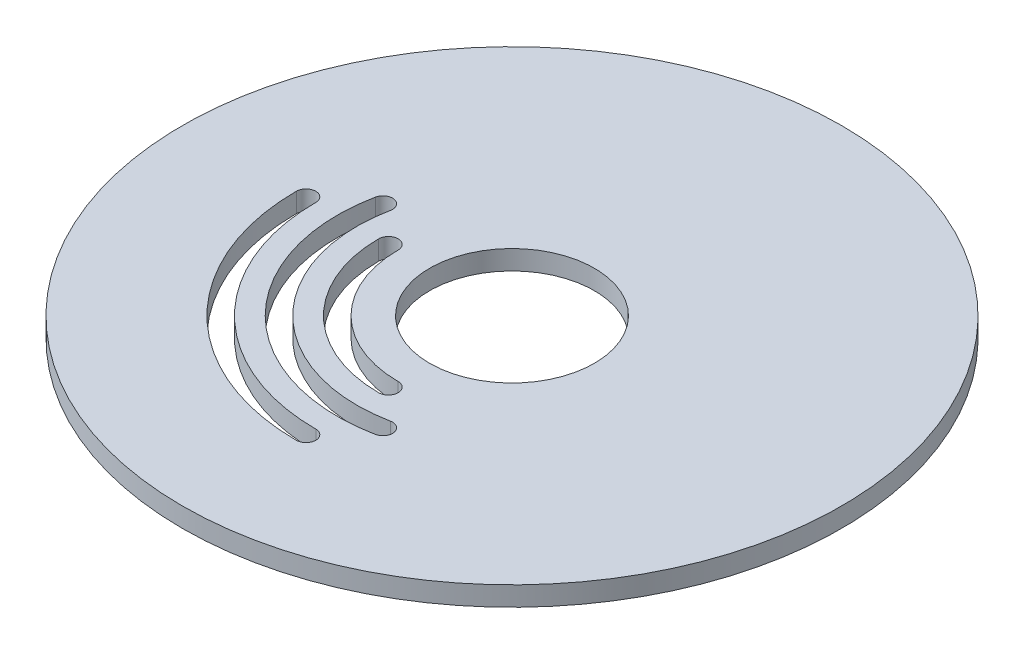
SolidWorks part; units mm, degrees
ref_plane "Front Plane" through (0, 0, 0) normal (0, 0, 1) x (1, 0, 0)
ref_plane "Top Plane" through (0, 0, 0) normal (0, 1, 0) x (1, 0, 0)
ref_plane "Right Plane" through (0, 0, 0) normal (1, 0, 0) x (0, 0, -1)
sketch "Sketch1" plane through (0, 0, 0) normal (0, 1, 0) x (1, 0, 0)
  circle A0 centre (0, 0) radius 50.8
  circle A1 centre (0, 0) radius 12.7
  arc A2 (-31.75, 0) -> (0, -31.75) centre (0, 0) ccw construction
  arc A3 (-33.25, 0) -> (0, -33.25) centre (0, 0) ccw
  arc A4 (-30.25, 0) -> (0, -30.25) centre (0, 0) ccw
  arc A5 (-30.25, 0) -> (-33.25, 0) centre (-31.75, 0) ccw
  arc A6 (0, -33.25) -> (0, -30.25) centre (0, -31.75) ccw
  arc A7 (-24.903, 5) -> (5, -24.903) centre (0, 0) ccw construction
  arc A8 (-26.3737, 5.2953) -> (5.2953, -26.3737) centre (0, 0) ccw
  arc A9 (-23.4324, 4.7047) -> (4.7047, -23.4324) centre (0, 0) ccw
  arc A10 (-23.4324, 4.7047) -> (-26.3737, 5.2953) centre (-24.903, 5) ccw
  arc A11 (5.2953, -26.3737) -> (4.7047, -23.4324) centre (5, -24.903) ccw
  arc A12 (-19.05, 0) -> (0, -19.05) centre (0, 0) ccw construction
  arc A13 (-20.55, 0) -> (0, -20.55) centre (0, 0) ccw
  arc A14 (-17.55, 0) -> (0, -17.55) centre (0, 0) ccw
  arc A15 (-17.55, 0) -> (-20.55, 0) centre (-19.05, 0) ccw
  arc A16 (0, -20.55) -> (0, -17.55) centre (0, -19.05) ccw
  point P6 (-22.4506, -22.4506)
  point P11 (-17.9605, -17.9605)
  point P19 (-13.4704, -13.4704)
  point P27 (0, 0)
  point P28 (0, 0)
  point P29 (0, 0)
  point P30 (0, 0)
  point P31 (0, 0)
  point P32 (0, 0)
  point P33 (0, 0)
  point P34 (0, 0)
  point P35 (0, 0)
  point P36 (5.8569, -24.7155)
  point P37 (0, 0)
  point P38 (0, 0)
  point P39 (0, 0)
  point P40 (-25.175, 3.214)
  point P41 (0, 0)
  point P42 (0, 0)
  point P43 (-25.1611, 3.4753)
  point P44 (0, 0)
  point P45 (3.3645, -25.1762)
  point P46 (-25.2349, 2.8911)
  point P47 (-24.5172, 6.6385)
  dimension "D1" = 25.4
  dimension "D2" = 101.6
  dimension "D4" = 19.05
  dimension "D6" = 3
  dimension "D7" = 3
  dimension "D8" = 3
  dimension "D3" = 25.4
  dimension "D5" = 31.75
  dimension "D9" = 5
  dimension "D10" = 5
extrude "Boss-Extrude1" add sketch "Sketch1" along normal blind 3
